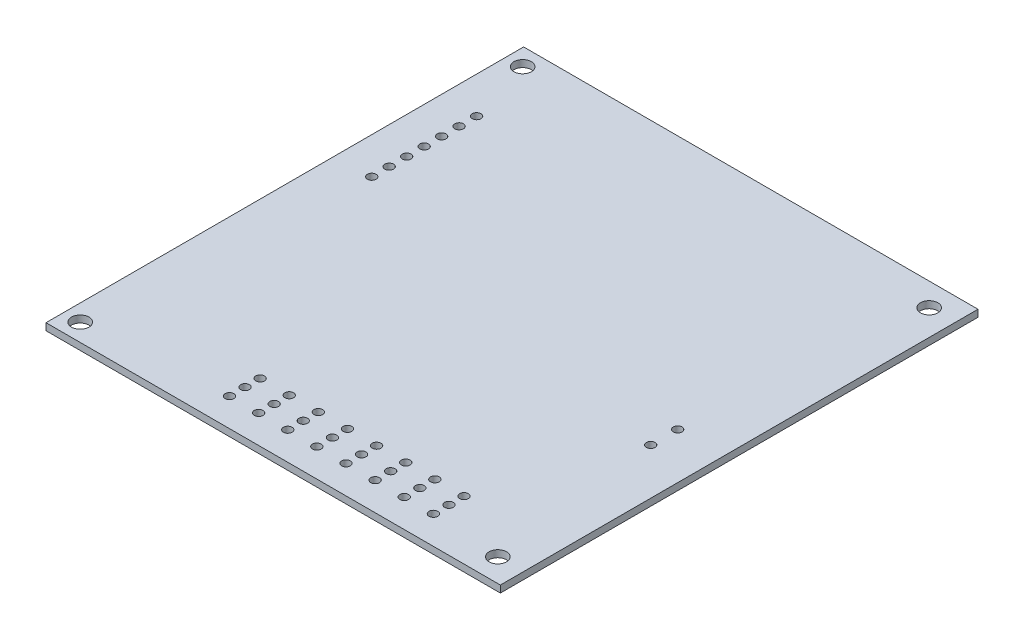
SolidWorks part; units mm, degrees
ref_plane "前视基准面" through (0, 0, 0) normal (0, 0, 1) x (1, 0, 0)
ref_plane "上视基准面" through (0, 0, 0) normal (0, 1, 0) x (1, 0, 0)
ref_plane "右视基准面" through (0, 0, 0) normal (1, 0, 0) x (0, 0, -1)
sketch "草图1" plane through (0, 0, 0) normal (0, 1, 0) x (1, 0, 0)
  line L5 (39, -41) -> (-39, -41)
  line L6 (39, -41) -> (39, 41)
  line L7 (39, 41) -> (-39, 41)
  line L8 (-39, -41) -> (-39, 41)
  line L9 (39, -41) -> (-39, 41) construction
  line L10 (39, 41) -> (-39, -41) construction
  point P0 (0, 0)
  dimension "D1" = 82
  dimension "D2" = 78
extrude "凸台-拉伸1" add sketch "草图1" along normal blind 1.2
sketch "草图2" plane through (0, 1.2, 0) normal (0, 1, 0) x (1, 0, 0)
  line L0 (50.1863, 0) -> (0, 0) construction
  line L1 (0, 0) -> (0, 32.059) construction
  circle A0 centre (34.5898, 37.0205) radius 1.5
  circle A1 centre (34.5898, -37.0205) radius 1.5
  circle A2 centre (-36.1492, 37.973) radius 1.5
  circle A3 centre (-36.1492, -37.973) radius 1.5
  dimension "D1" = 3
  dimension "D2" = 74.041
  dimension "D3" = 75.946
  dimension "D4" = 70.739
extrude "切除-拉伸1" cut sketch "草图2" against normal through all contours A2 | A0 | A3 | A1
sketch "草图3" plane through (0, 1.2, 0) normal (0, 1, 0) x (1, 0, 0)
  text T0 "1" font "汉仪长仿宋体" height 5.5
  text T1 "2" font "汉仪长仿宋体" height 5.5
  text T2 "3" font "汉仪长仿宋体" height 5.5
  text T3 "4" font "汉仪长仿宋体" height 5.5
  text T4 "传感器接口" font "汉仪长仿宋体" height 2.5
  text T5 "电机驱动部分" font "汉仪长仿宋体" height 2.5
sketch "草图4" plane through (0, 1.2, 0) normal (0, 1, 0) x (1, 0, 0)
  circle A0 centre (31.088, -2.6437) radius 0.75
  circle A1 centre (31.088, -7.2742) radius 0.75
  circle A2 centre (-32.7394, 26.66) radius 0.75
  circle A3 centre (22.6668, -30.9116) radius 0.75
  circle A4 centre (22.6668, -33.4924) radius 0.75
  circle A5 centre (22.6668, -36.1622) radius 0.75
  circle A6 centre (17.6668, -36.1622) radius 0.75
  circle A7 centre (17.6668, -33.4924) radius 0.75
  circle A8 centre (17.6668, -30.9116) radius 0.75
  circle A9 centre (12.6668, -36.1622) radius 0.75
  circle A10 centre (12.6668, -33.4924) radius 0.75
  circle A11 centre (12.6668, -30.9116) radius 0.75
  circle A12 centre (7.6668, -36.1622) radius 0.75
  circle A13 centre (7.6668, -33.4924) radius 0.75
  circle A14 centre (7.6668, -30.9116) radius 0.75
  circle A15 centre (2.6668, -36.1622) radius 0.75
  circle A16 centre (2.6668, -33.4924) radius 0.75
  circle A17 centre (2.6668, -30.9116) radius 0.75
  circle A18 centre (-2.3332, -36.1622) radius 0.75
  circle A19 centre (-2.3332, -33.4924) radius 0.75
  circle A20 centre (-2.3332, -30.9116) radius 0.75
  circle A21 centre (-7.3332, -36.1622) radius 0.75
  circle A22 centre (-7.3332, -33.4924) radius 0.75
  circle A23 centre (-7.3332, -30.9116) radius 0.75
  circle A24 centre (-12.3332, -36.1622) radius 0.75
  circle A25 centre (-12.3332, -33.4924) radius 0.75
  circle A26 centre (-12.3332, -30.9116) radius 0.75
  circle A27 centre (-32.7394, 23.66) radius 0.75
  circle A28 centre (-32.7394, 20.66) radius 0.75
  circle A29 centre (-32.7394, 17.66) radius 0.75
  circle A30 centre (-32.7394, 14.66) radius 0.75
  circle A31 centre (-32.7394, 11.66) radius 0.75
  circle A32 centre (-32.7394, 8.66) radius 0.75
  dimension "D1" = 1.5
  dimension "D2" = 8
  dimension "D3" = 7
extrude "切除-拉伸2" cut sketch "草图4" against normal through all
